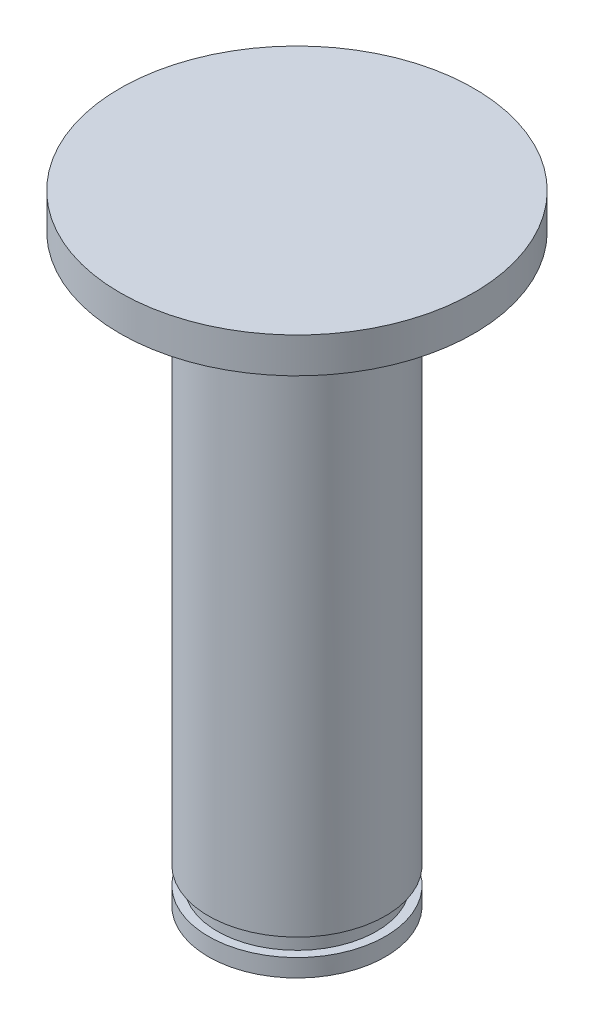
SolidWorks part; units mm, degrees
material "AISI 1018"
ref_plane "Alzado" through (0, 0, 0) normal (0, 0, 1) x (1, 0, 0)
ref_plane "Planta" through (0, 0, 0) normal (0, 1, 0) x (1, 0, 0)
ref_plane "Vista lateral" through (0, 0, 0) normal (1, 0, 0) x (0, 0, -1)
sketch "Croquis1" plane through (0, 0, 0) normal (0, 1, 0) x (1, 0, 0)
  circle A0 centre (0, 0) radius 5
  dimension "D1" = 10
extrude "Saliente-Extruir1" add sketch "Croquis1" along normal blind 33
sketch "Croquis2" plane through (0, 33, 0) normal (0, 1, 0) x (1, 0, 0)
  circle A0 centre (0, 0) radius 10
  dimension "D1" = 20
extrude "Saliente-Extruir2" add sketch "Croquis2" along normal blind 2
ref_plane "Plane1" through (0, 2, 0) normal (0, -1, 0) x (-1, 0, 0)
sketch "Sketch3" plane through (0, 2, 0) normal (0, -1, 0) x (-1, 0, 0)
  circle A0 centre (0, 0) radius 5 construction
  circle A1 centre (0, 0) radius 5
  circle A2 centre (0, 0) radius 4.5
  dimension "D1" = 0.5
extrude "Cut-Extrude1" cut sketch "Sketch3" along normal blind 1
